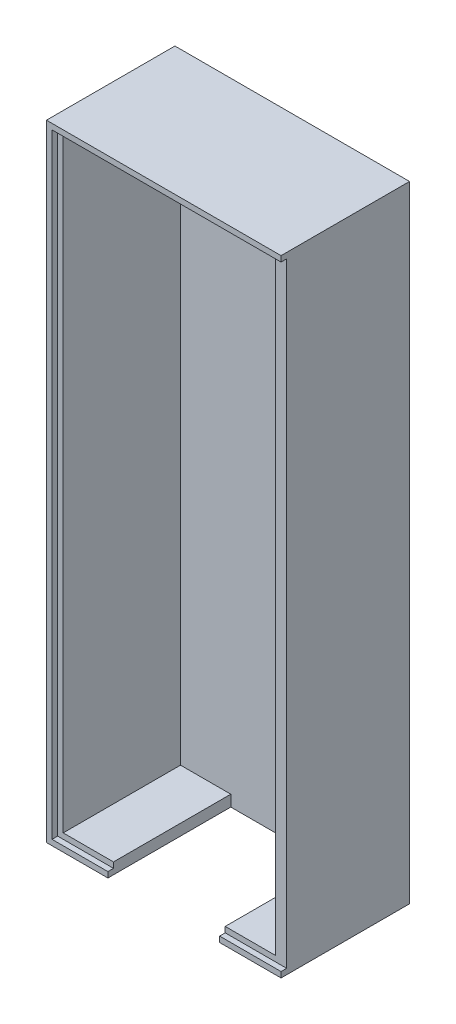
SolidWorks part; units mm, degrees
ref_plane "정면" through (0, 0, 0) normal (0, 0, 1) x (1, 0, 0)
ref_plane "윗면" through (0, 0, 0) normal (0, 1, 0) x (1, 0, 0)
ref_plane "우측면" through (0, 0, 0) normal (1, 0, 0) x (0, 0, -1)
sketch "스케치1" plane through (0, 0, 0) normal (0, 0, 1) x (1, 0, 0)
  line L1 (0, 0) -> (40, 0)
  line L2 (0, 0) -> (0, 110)
  line L3 (0, 110) -> (40, 110)
  line L4 (40, 0) -> (40, 110)
  dimension "D1" = 110
  dimension "D2" = 40
extrude "보스-돌출1" add sketch "스케치1" along normal blind 22
shell "쉘1" thickness 1
sketch "스케치17" plane through (0, 1, 0) normal (0, 1, 0) x (1, 0, 0)
  line L0 (1, -1) -> (39, -1) construction
  line L1 (10, -1) -> (30, -1)
  line L2 (10, -1) -> (10, -22)
  line L3 (10, -22) -> (30, -22)
  line L4 (30, -1) -> (30, -22)
  line L5 (1, -22) -> (39, -22) construction
  line L6 (1, -22) -> (1, -1) construction
  dimension "D1" = 20
  dimension "D2" = 9
extrude "컷-돌출3" cut sketch "스케치17" against normal through all
sketch "스케치2" plane through (0, 0, 0) normal (-1, 0, 0) x (0, 0, 1)
  line L1 (0, 0) -> (23, 0)
  line L2 (0, 0) -> (0, 110)
  line L3 (0, 110) -> (23, 110)
  line L4 (23, 0) -> (23, 110)
  dimension "D1" = 110
  dimension "D2" = 23
extrude "보스-돌출2" add sketch "스케치2" along normal blind 1
sketch "스케치3" plane through (0, 0, 0) normal (0, -1, 0) x (1, 0, 0)
  line L1 (-1, 0) -> (40, 0)
  line L2 (-1, 0) -> (-1, 23)
  line L3 (-1, 23) -> (40, 23)
  line L4 (40, 0) -> (40, 23)
  dimension "D1" = 41
  dimension "D2" = 23
extrude "보스-돌출3" add sketch "스케치3" along normal blind 1
sketch "스케치18" plane through (0, 0, 0) normal (0, 1, 0) x (1, 0, 0)
  line L0 (40, -23) -> (0, -23) construction
  line L1 (10, -1) -> (30, -1)
  line L2 (10, -1) -> (10, -23)
  line L3 (10, -23) -> (30, -23)
  line L4 (30, -1) -> (30, -23)
  dimension "D1" = 20
extrude "컷-돌출4" cut sketch "스케치18" against normal through all
sketch "스케치5" plane through (0, 110, 0) normal (0, 1, 0) x (1, 0, 0)
  line L1 (-1, -23) -> (40, -23)
  line L2 (-1, -23) -> (-1, 0)
  line L3 (-1, 0) -> (40, 0)
  line L4 (40, -23) -> (40, 0)
extrude "보스-돌출4" add sketch "스케치5" along normal blind 1
sketch "스케치9" plane through (40, 0, 0) normal (1, 0, 0) x (0, 0, -1)
  line L0 (-23, 111) -> (0, 111) construction
  line L1 (0, -1) -> (-22, -1)
  line L2 (0, -1) -> (0, 111)
  line L3 (0, 111) -> (-22, 111)
  line L4 (-22, -1) -> (-22, 111)
  dimension "D1" = 22
extrude "보스-돌출5" add sketch "스케치9" along normal blind 1
sketch "스케치10" plane through (0, 0, 22) normal (0, 0, 1) x (1, 0, 0)
  line L0 (41, 111) -> (41, -1) construction
  line L1 (40, 111) -> (41, 111)
  line L2 (40, 111) -> (40, 110)
  line L3 (40, 110) -> (41, 110)
  line L4 (41, 111) -> (41, 110)
extrude "보스-돌출6" add sketch "스케치10" along normal blind 1
sketch "스케치11" plane through (0, 0, 22) normal (0, 0, 1) x (1, 0, 0)
  line L1 (40, 0) -> (41, 0)
  line L2 (40, 0) -> (40, -1)
  line L3 (40, -1) -> (41, -1)
  line L4 (41, 0) -> (41, -1)
extrude "보스-돌출7" add sketch "스케치11" along normal blind 1
